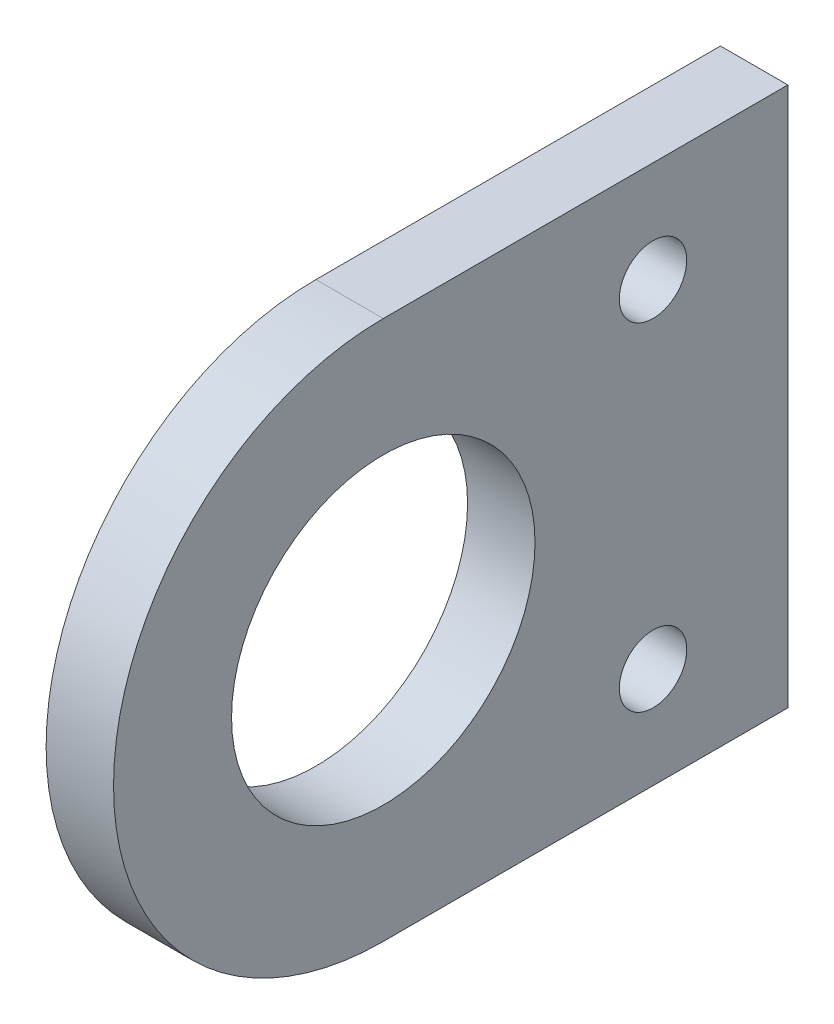
SolidWorks part; units mm, degrees
material "6061-T6 (SS)"
ref_plane "Front Plane" through (0, 0, 0) normal (0, 0, 1) x (1, 0, 0)
ref_plane "Top Plane" through (0, 0, 0) normal (0, 1, 0) x (1, 0, 0)
ref_plane "Right Plane" through (0, 0, 0) normal (1, 0, 0) x (0, 0, -1)
sketch "Sketch1" plane through (0, 0, 0) normal (1, 0, 0) x (0, 0, -1)
  line L0 (0, 25.4) -> (38.1, 25.4)
  line L1 (38.1, 25.4) -> (38.1, -25.4)
  line L2 (38.1, -25.4) -> (0, -25.4)
  line L3 (25.4, 15.875) -> (25.4, -15.875) construction
  line L4 (25.4, 0) -> (38.1, 0) construction
  circle A0 centre (0, 0) radius 14.2875
  arc A1 (0, -25.4) -> (0, 25.4) centre (0, 0) cw
  circle A2 centre (25.4, 15.875) radius 3.175
  circle A3 centre (25.4, -15.875) radius 3.175
  dimension "D1" = 28.575
  dimension "D2" = 50.8
  dimension "D6" = 6.35
  dimension "D3" = 38.1
  dimension "D4" = 31.75
  dimension "D5" = 12.7
extrude "Boss-Extrude1" add sketch "Sketch1" along normal blind 6.35
